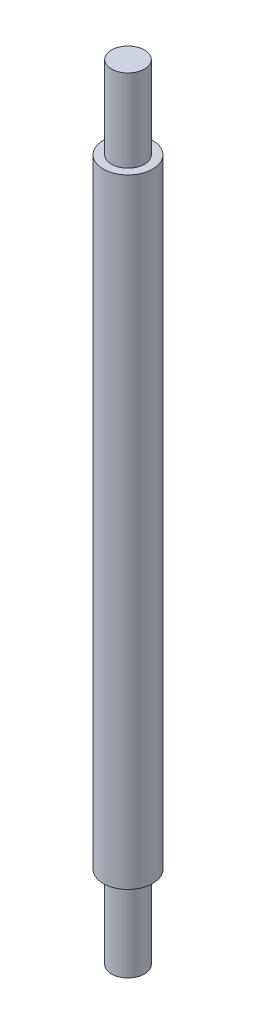
SolidWorks part; units mm, degrees
ref_plane "Front Plane" through (0, 0, 0) normal (0, 0, 1) x (1, 0, 0)
ref_plane "Top Plane" through (0, 0, 0) normal (0, 1, 0) x (1, 0, 0)
ref_plane "Right Plane" through (0, 0, 0) normal (1, 0, 0) x (0, 0, -1)
sketch "Sketch1" plane through (0, 0, 0) normal (0, 1, 0) x (1, 0, 0)
  circle A0 centre (0, 0) radius 3
extrude "Boss-Extrude1" add sketch "Sketch1" along normal blind 75
sketch "Sketch2" plane through (0, 75, 0) normal (0, 1, 0) x (1, 0, 0)
  circle A0 centre (0, 0) radius 2
extrude "Boss-Extrude2" add sketch "Sketch2" along normal blind 10
sketch "Sketch3" plane through (0, 0, 0) normal (0, -1, 0) x (1, 0, 0)
  circle A0 centre (0, 0) radius 2
extrude "Boss-Extrude3" add sketch "Sketch3" along normal blind 10
